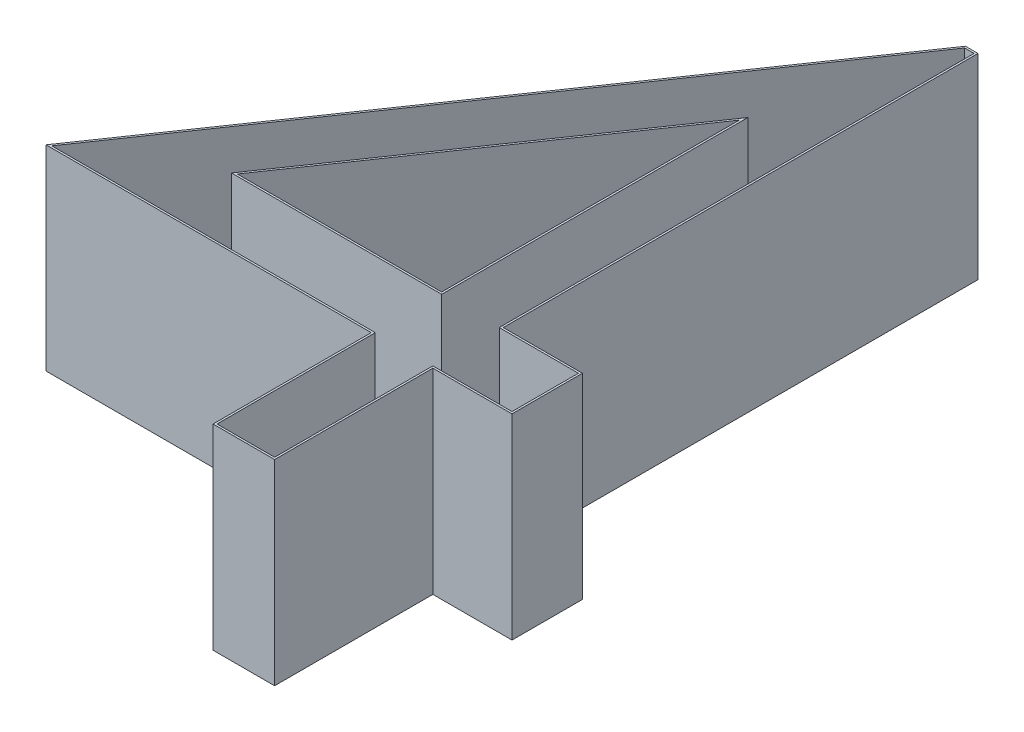
SolidWorks part; units mm, degrees
ref_plane "Front Plane" through (0, 0, 0) normal (0, 0, 1) x (1, 0, 0)
ref_plane "Top Plane" through (0, 0, 0) normal (0, 1, 0) x (1, 0, 0)
ref_plane "Right Plane" through (0, 0, 0) normal (1, 0, 0) x (0, 0, -1)
sketch "Sketch1" plane through (0, 0, 0) normal (0, 1, 0) x (1, 0, 0)
  text T0 "4\r\n"
extrude "Boss-Extrude1" add sketch "Sketch1" along normal blind 1
sketch "Sketch2" plane through (0, 1, 0) normal (0, 1, 0) x (1, 0, 0)
  line L19 (0.7326, 1.1567) -> (1.8049, 1.1567)
  line L20 (2.0504, 3.5797) -> (0.1536, 0.8177)
  line L21 (0.1536, 0.8177) -> (1.8049, 0.8177)
  line L22 (1.8049, 0.8177) -> (1.8049, 0.01)
  line L23 (1.8049, 0.01) -> (2.099, 0.01)
  line L24 (2.099, 0.01) -> (2.099, 0.8177)
  line L25 (2.099, 0.8177) -> (2.5028, 0.8177)
  line L26 (2.5028, 0.8177) -> (2.5028, 1.1567)
  line L27 (2.5028, 1.1567) -> (2.099, 1.1567)
  line L28 (2.099, 1.1567) -> (2.099, 3.5797)
  line L29 (2.099, 3.5797) -> (2.0504, 3.5797)
  line L30 (2.0504, 3.5797) -> (0.1536, 0.8177)
  line L31 (0.1536, 0.8177) -> (1.8049, 0.8177)
  line L32 (1.8049, 0.8177) -> (1.8049, 0.01)
  line L33 (1.8049, 0.01) -> (2.099, 0.01)
  line L34 (2.099, 0.01) -> (2.099, 0.8177)
  line L35 (2.099, 0.8177) -> (2.5028, 0.8177)
  line L36 (2.5028, 0.8177) -> (2.5028, 1.1567)
  line L37 (2.5028, 1.1567) -> (2.099, 1.1567)
  line L38 (2.099, 1.1567) -> (2.099, 3.5797)
  line L39 (2.099, 3.5797) -> (2.0504, 3.5797)
  line L40 (1.8049, 1.1567) -> (1.8049, 2.7189)
  line L41 (1.8049, 2.7189) -> (0.7326, 1.1567)
  line L42 (0.7326, 1.1567) -> (1.8049, 1.1567)
  line L43 (1.8049, 1.1567) -> (1.8049, 2.7189)
  line L44 (1.8049, 2.7189) -> (0.7326, 1.1567)
  dimension "D1" = 0.01
  dimension "D2" = 0.01
extrude "Cut-Extrude2" cut sketch "Sketch2" against normal blind 1
